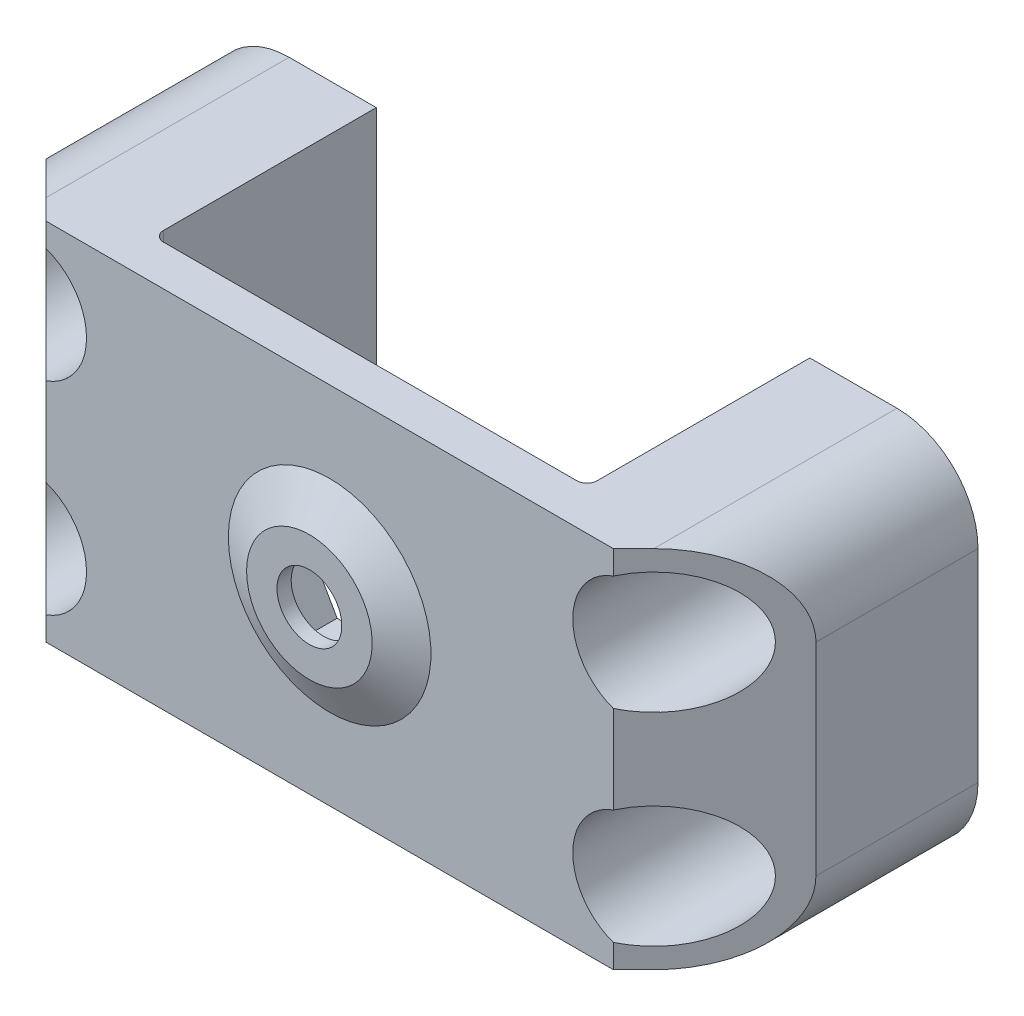
SolidWorks part; units mm, degrees
ref_plane "Front Plane" through (0, 0, 0) normal (0, 0, 1) x (1, 0, 0)
ref_plane "Top Plane" through (0, 0, 0) normal (0, 1, 0) x (1, 0, 0)
ref_plane "Right Plane" through (0, 0, 0) normal (1, 0, 0) x (0, 0, -1)
sketch "Sketch1" plane through (0, 0, 0) normal (0, 1, 0) x (1, 0, 0)
  line L0 (10.7, 13) -> (19, 13)
  line L1 (-19, 13) -> (-10.7, 13)
  line L2 (-19, 13) -> (-19, 0)
  line L3 (-19, 0) -> (19, 0)
  line L4 (19, 13) -> (19, 0)
  line L6 (-10.7, 13) -> (-10.7, 2)
  line L7 (-10.7, 2) -> (10.7, 2)
  line L8 (10.7, 13) -> (10.7, 2)
  point P7 (0, 2)
  point P9 (0, 0)
  dimension "D1" = 2
  dimension "D2" = 21.4
  dimension "D3" = 38
  dimension "D4" = 11
extrude "Boss-Extrude1" add sketch "Sketch1" along normal mid plane 18
sketch "Sketch2" plane through (0, 0, -13) normal (0, 0, -1) x (-1, 0, 0)
  line L1 (-15, -5) -> (15, -5) construction
  line L2 (-15, -5) -> (-15, 5) construction
  line L3 (-15, 5) -> (15, 5) construction
  line L4 (15, -5) -> (15, 5) construction
  line L5 (-15, -5) -> (15, 5) construction
  line L6 (-15, 5) -> (15, -5) construction
  circle A0 centre (-15, 5) radius 1.6
  circle A1 centre (-15, -5) radius 1.6
  circle A2 centre (15, 5) radius 1.6
  circle A3 centre (15, -5) radius 1.6
  point P0 (0, 0)
  dimension "D3" = 3.2
  dimension "D1" = 30
  dimension "D2" = 10
extrude "Cut-Extrude1" cut sketch "Sketch2" against normal through all
sketch "Sketch3" plane through (0, 0, -2) normal (0, 0, -1) x (-1, 0, 0)
  circle A0 centre (0, 0) radius 1.6
  dimension "D1" = 3.2
extrude "Cut-Extrude2" cut sketch "Sketch3" against normal through all
sketch "Sketch9" plane through (0, 0, 0) normal (1, 0, 0) x (0, 0, -1)
  line L0 (0, 1.6) -> (0, 5)
  line L1 (0, 5) -> (-1, 3.1)
  line L2 (-1, 1.6) -> (0, 1.6)
  line L3 (-1, 1.6) -> (-1, 3.1)
  line L4 (0, 0) -> (-4.1877, 0) construction
  dimension "D1" = 1
  dimension "D2" = 1.5
  dimension "D3" = 10
revolve "Revolve1" add sketch "Sketch9" angle 360 about L4
sketch "Sketch4" plane through (0, 0, -2) normal (0, 0, -1) x (-1, 0, 0)
  line L1 (1.602, 2.8083) -> (-1.6311, 2.7916)
  line L2 (-1.6311, 2.7916) -> (-3.2331, -0.0168)
  line L3 (-3.2331, -0.0168) -> (-1.602, -2.8083)
  line L4 (-1.602, -2.8083) -> (1.6311, -2.7916)
  line L5 (1.6311, -2.7916) -> (3.2331, 0.0168)
  line L6 (3.2331, 0.0168) -> (1.602, 2.8083)
  circle A0 centre (0, 0) radius 2.8 construction
  dimension "D1" = 5.6
extrude "Cut-Extrude3" cut sketch "Sketch4" against normal blind 2.3
sketch "Sketch10" plane through (0, 0, 0) normal (0, 1, 0) x (1, 0, 0)
  line L0 (-19, 0) -> (-19, 5)
  line L1 (-19, 5) -> (-14, 0)
  line L2 (-14, 0) -> (-19, 0)
  line L3 (0, 0) -> (0, 8.4574) construction
  line L4 (14, 0) -> (19, 0)
  line L5 (19, 0) -> (19, 5)
  line L6 (19, 5) -> (14, 0)
  dimension "D1" = 5
extrude "Cut-Extrude4" cut sketch "Sketch10" against normal through all and the other way through all
fillet "Fillet2" radius 4 4 edges at (19, -9, -9) (19, 9, -9) (-19, -9, -9) (-19, 9, -9)
fillet "Fillet5" radius 0.5 2 edges at (-10.7, 0, -2) (10.7, 0, -2)
sketch "Sketch11" plane through (0, 0, 0) normal (0, 0, 1) x (1, 0, 0)
  circle A0 centre (-15, 5) radius 3
  circle A1 centre (-15, -5) radius 3
  circle A2 centre (15, 5) radius 3
  circle A3 centre (15, -5) radius 3
  dimension "D1" = 6
extrude "Cut-Extrude5" cut sketch "Sketch11" against normal offset from surface (11 mm away) 2 up to face at (-16.6, -5, -13)
